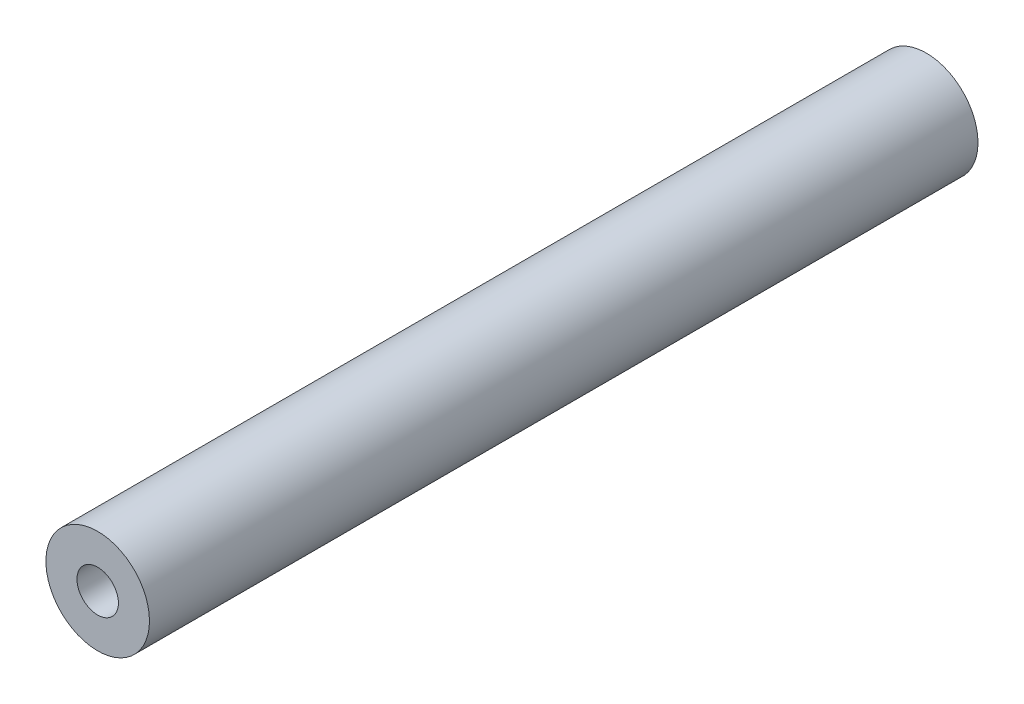
SolidWorks part; units mm, degrees
ref_plane "Alzado" through (0, 0, 0) normal (0, 0, 1) x (1, 0, 0)
ref_plane "Planta" through (0, 0, 0) normal (0, 1, 0) x (1, 0, 0)
ref_plane "Vista lateral" through (0, 0, 0) normal (1, 0, 0) x (0, 0, -1)
sketch "Croquis1" plane through (0, 0, 0) normal (0, 0, 1) x (1, 0, 0)
  circle A0 centre (0, 0) radius 10
  circle A1 centre (0, 0) radius 25
  dimension "D1" = 50
  dimension "D2" = 20
extrude "Saliente-Extruir1" add sketch "Croquis1" along normal blind 400
